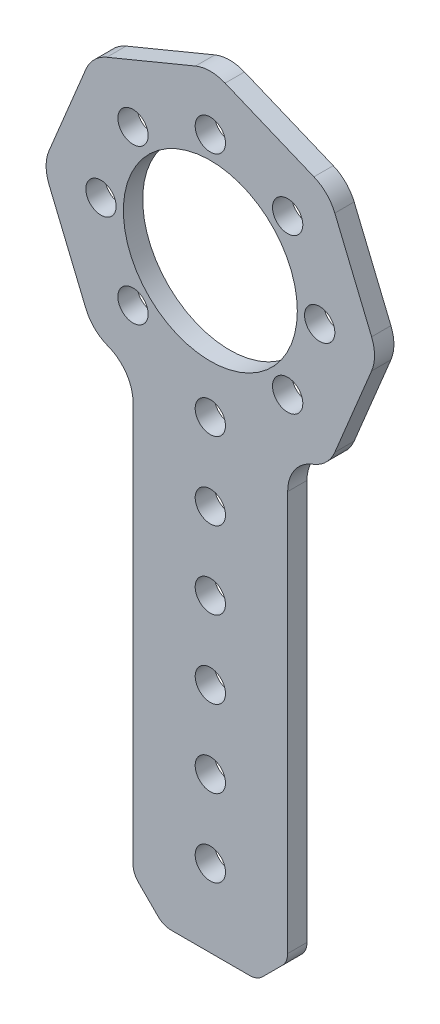
SolidWorks part; units mm, degrees
material "5052-H32"
ref_plane "Front Plane" through (0, 0, 0) normal (0, 0, 1) x (1, 0, 0)
ref_plane "Top Plane" through (0, 0, 0) normal (0, 1, 0) x (1, 0, 0)
ref_plane "Right Plane" through (0, 0, 0) normal (1, 0, 0) x (0, 0, -1)
ref_plane "Plane1" through (0, 0, -3.175) normal (0, 0, -1) x (-1, 0, 0)
sketch "Sketch1" plane through (0, 0, -3.175) normal (0, 0, -1) x (-1, 0, 0)
  line L0 (8.5787, -97.5536) -> (11.8213, -94.3109)
  line L1 (12.7, -92.1896) -> (12.7, -26.4752)
  line L2 (16.62, -20.6085) -> (17.0103, -20.4469)
  line L3 (20.4469, -17.0103) -> (26.4862, -2.43)
  line L4 (26.4862, 2.43) -> (20.4469, 17.0103)
  line L5 (17.0103, 20.4469) -> (2.43, 26.4862)
  line L6 (-2.43, 26.4862) -> (-17.0103, 20.4469)
  line L7 (-20.4469, 17.0103) -> (-26.4862, 2.43)
  line L8 (-26.4862, -2.43) -> (-20.4469, -17.0103)
  line L9 (-17.0103, -20.4469) -> (-16.62, -20.6085)
  line L10 (-12.7, -26.4752) -> (-12.7, -92.1896)
  line L11 (-11.8213, -94.3109) -> (-8.5787, -97.5536)
  line L12 (-6.4574, -98.4322) -> (6.4574, -98.4322)
  circle A0 centre (12.7, -12.7) radius 2.4892
  circle A1 centre (0, 0) radius 14.2875
  circle A2 centre (-12.7, 12.7) radius 2.4892
  circle A3 centre (-17.9605, 0) radius 2.4892
  circle A4 centre (-12.7, -12.7) radius 2.4892
  circle A5 centre (12.7, 12.7) radius 2.4892
  circle A6 centre (17.9605, 0) radius 2.4892
  circle A7 centre (0, 17.9605) radius 2.4892
  circle A8 centre (0, -22.2322) radius 2.4892
  circle A9 centre (0, -73.0322) radius 2.4892
  circle A10 centre (0, -47.6322) radius 2.4892
  circle A11 centre (0, -34.9322) radius 2.4892
  circle A12 centre (0, -60.3322) radius 2.4892
  circle A13 centre (0, -85.7322) radius 2.4892
  arc A14 (11.8213, -94.3109) -> (12.7, -92.1896) centre (9.7, -92.1896) ccw
  arc A15 (12.7, -26.4752) -> (16.62, -20.6085) centre (19.05, -26.4752) cw
  arc A16 (17.0103, -20.4469) -> (20.4469, -17.0103) centre (14.5802, -14.5802) ccw
  arc A17 (26.4862, -2.43) -> (26.4862, 2.43) centre (20.6196, 0) ccw
  arc A18 (20.4469, 17.0103) -> (17.0103, 20.4469) centre (14.5802, 14.5802) ccw
  arc A19 (2.43, 26.4862) -> (-2.43, 26.4862) centre (0, 20.6196) ccw
  arc A20 (-17.0103, 20.4469) -> (-20.4469, 17.0103) centre (-14.5802, 14.5802) ccw
  arc A21 (-26.4862, 2.43) -> (-26.4862, -2.43) centre (-20.6196, 0) ccw
  arc A22 (-20.4469, -17.0103) -> (-17.0103, -20.4469) centre (-14.5802, -14.5802) ccw
  arc A23 (-16.62, -20.6085) -> (-12.7, -26.4752) centre (-19.05, -26.4752) cw
  arc A24 (-12.7, -92.1896) -> (-11.8213, -94.3109) centre (-9.7, -92.1896) ccw
  arc A25 (-8.5787, -97.5536) -> (-6.4574, -98.4322) centre (-6.4574, -95.4322) ccw
  arc A26 (6.4574, -98.4322) -> (8.5787, -97.5536) centre (6.4574, -95.4322) ccw
  point P67 (0, 0)
  point P68 (0, 0)
  point P69 (0, 0)
  point P70 (0, 0)
  point P71 (0, 0)
  dimension "D1" = 3
  dimension "D2" = 6.35
  dimension "D3" = 6.35
  dimension "D4" = 3
  dimension "D5" = 0.8787
  dimension "D6" = 4.1213
  dimension "D7" = 10.27
  dimension "D8" = 12.7
  dimension "D9" = 27.2802
  dimension "D10" = 1.8802
  dimension "D11" = 12.7
  dimension "D12" = 25.4
  dimension "D13" = 38.1
  dimension "D14" = 50.8
  dimension "D15" = 63.5
  dimension "D16" = 96.0022
  dimension "D17" = 76.2
  dimension "D19" = 30.6605
  dimension "D23" = 85.7322
  dimension "D26" = 5.2605
  dimension "D28" = 111.1322
  dimension "D31" = 116.3928
extrude "Boss-Extrude1" add sketch "Sketch1" against normal blind 3.175
